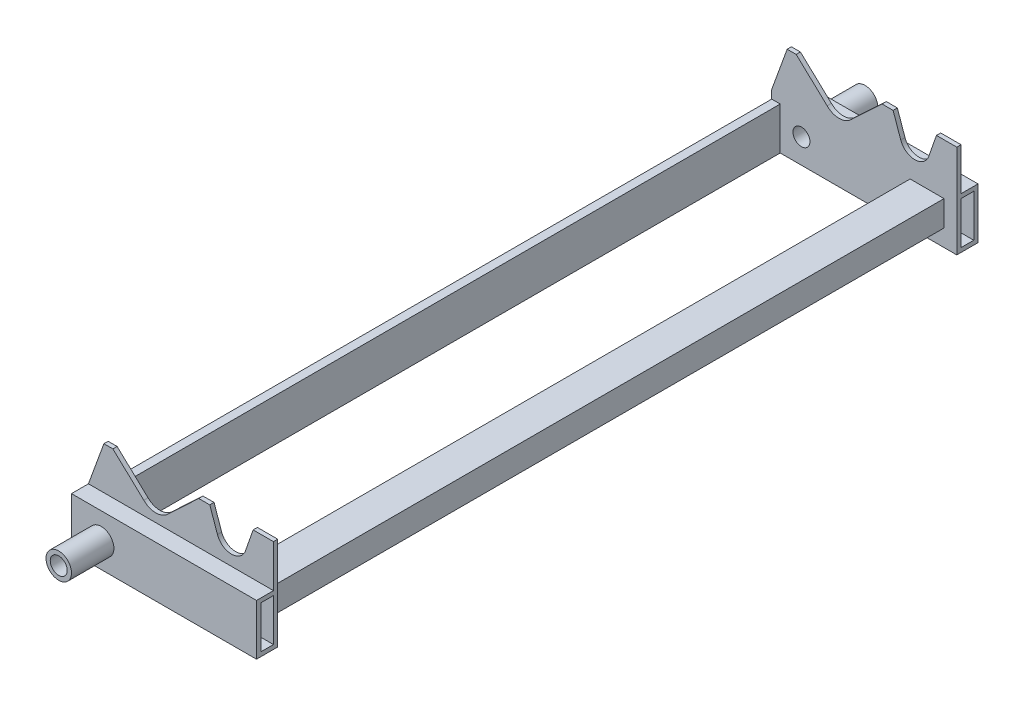
SolidWorks part; units mm, degrees
ref_plane "Front Plane" through (0, 0, 0) normal (0, 0, 1) x (1, 0, 0)
ref_plane "Top Plane" through (0, 0, 0) normal (0, 1, 0) x (1, 0, 0)
ref_plane "Right Plane" through (0, 0, 0) normal (1, 0, 0) x (0, 0, -1)
sketch "Sketch3" plane through (0, 0, 0) normal (0, 0, 1) x (1, 0, 0)
  line L0 (-86.5455, 46) -> (131.4545, 46)
  line L1 (-86.5455, 46) -> (131.4545, 46)
  line L3 (131.4545, 0) -> (131.4545, 76)
  line L6 (-51.5455, 0) -> (-51.5455, 15) construction
  line L8 (-7.1805, 76) -> (-7.1805, 61)
  line L9 (22.4547, 76) -> (23.8195, 76)
  line L11 (43.3957, 96) -> (56.4426, 96)
  line L12 (-86.5455, 0) -> (-86.5455, 46)
  line L13 (-86.5455, 46) -> (-68.3469, 96)
  line L14 (-7.1805, 61) -> (-7.1805, 56)
  line L15 (-7.1805, 91) -> (-7.1805, 96)
  line L18 (-68.3469, 96) -> (-57.7539, 96)
  line L19 (-57.7539, 96) -> (-21.3226, 61.8579)
  line L20 (6.9617, 61.8579) -> (43.3957, 96)
  line L21 (56.4426, 96) -> (65.4492, 70.2268)
  line L22 (107.4965, 96) -> (131.4545, 96)
  line L23 (98.4899, 70.2268) -> (107.4965, 96)
  line L24 (131.4545, 96) -> (131.4545, 76)
  line L25 (-86.5455, 0) -> (-86.5455, -14)
  line L26 (-86.5455, -14) -> (131.4545, -14)
  line L27 (131.4545, -14) -> (131.4545, 0)
  arc A3 (65.4492, 70.2268) -> (98.4899, 70.2268) centre (81.9695, 76) ccw
  arc A5 (-21.3226, 61.8579) -> (6.9617, 61.8579) centre (-7.1805, 76) ccw
  circle A6 centre (-51.5455, 15) radius 15
  circle A7 centre (-51.5455, 15) radius 10
  dimension "D1" = 35
  dimension "D2" = 30
  dimension "D3" = 89.15
  dimension "D4" = 46
  dimension "D9" = 5
  dimension "D13" = 14
  dimension "D8" = 17.5
  dimension "D5" = 15
  dimension "D6" = 160
  dimension "D7" = 5
extrude "Boss-Extrude1" add sketch "Sketch3" along normal blind 25
sketch "Sketch5" plane through (0, 0, 25) normal (0, 0, 1) x (1, 0, 0)
  line L0 (-86.5455, 46) -> (131.4545, 46)
  line L1 (131.4545, -14) -> (131.4545, 96) construction
  line L2 (131.4545, 46) -> (131.4545, 96)
  line L3 (131.4545, 96) -> (-86.5455, 96)
  line L4 (-86.5455, 96) -> (-86.5455, 46)
extrude "Cut-Extrude1" cut sketch "Sketch5" against normal blind 20
sketch "Sketch7" plane through (-86.5455, 0, 0) normal (-1, 0, 0) x (0, 0, 1)
  line L0 (25, 46) -> (5, 46) construction
  line L1 (5, 41) -> (20, 41)
  line L2 (5, 41) -> (5, -9)
  line L3 (5, -9) -> (20, -9)
  line L4 (20, 41) -> (20, -9)
  line L5 (25, -14) -> (25, 46) construction
  line L6 (25, -14) -> (0, -14) construction
  line L7 (0, -14) -> (0, 46) construction
  dimension "D1" = 5
  dimension "D2" = 5
  dimension "D3" = 5
  dimension "D4" = 5
extrude "Cut-Extrude3" cut sketch "Sketch7" against normal through all
sketch "Sketch8" plane through (0, 0, 0) normal (0, 0, -1) x (-1, 0, 0)
  circle A0 centre (51.5455, 15) radius 10
  circle A1 centre (51.5455, 15) radius 15
extrude "Boss-Extrude7" add sketch "Sketch8" against normal blind 75
sketch "Sketch9" plane through (0, 0, 0) normal (0, 0, -1) x (-1, 0, 0)
  line L8 (86.5455, -14) -> (76.5455, -14)
  line L9 (86.5455, -14) -> (86.5455, 36)
  line L10 (86.5455, 36) -> (76.5455, 36)
  line L11 (76.5455, -14) -> (76.5455, 36)
  dimension "D1" = 10
  dimension "D2" = 50
extrude "Boss-Extrude8" add sketch "Sketch9" along normal blind 400
sketch "Sketch10" plane through (0, 0, 0) normal (0, 0, -1) x (-1, 0, 0)
  line L0 (-131.4545, -14) -> (-131.4545, 96) construction
  line L9 (-116.4545, 36) -> (-76.4545, 36)
  line L10 (-116.4545, 36) -> (-116.4545, 6)
  line L11 (-116.4545, 6) -> (-76.4545, 6)
  line L12 (-76.4545, 36) -> (-76.4545, 6)
  line L13 (76.5455, -14) -> (-131.4545, -14) construction
  line L15 (-113.4545, 33) -> (-79.4545, 33)
  line L16 (-113.4545, 33) -> (-113.4545, 9)
  line L17 (-113.4545, 9) -> (-79.4545, 9)
  line L18 (-79.4545, 33) -> (-79.4545, 9)
  dimension "D1" = 15
  dimension "D2" = 20
  dimension "D3" = 40
  dimension "D4" = 30
  dimension "D5" = 3
  dimension "D6" = 3
  dimension "D7" = 3
  dimension "D8" = 3
extrude "Boss-Extrude9" add sketch "Sketch10" along normal blind 400
ref_plane "Plane1" through (0, 0, -400) normal (0, 0, -1) x (-1, 0, 0)
mirror "Mirror1" about plane through (0, 0, -400) normal (0, 0, -1) of bodies 128
